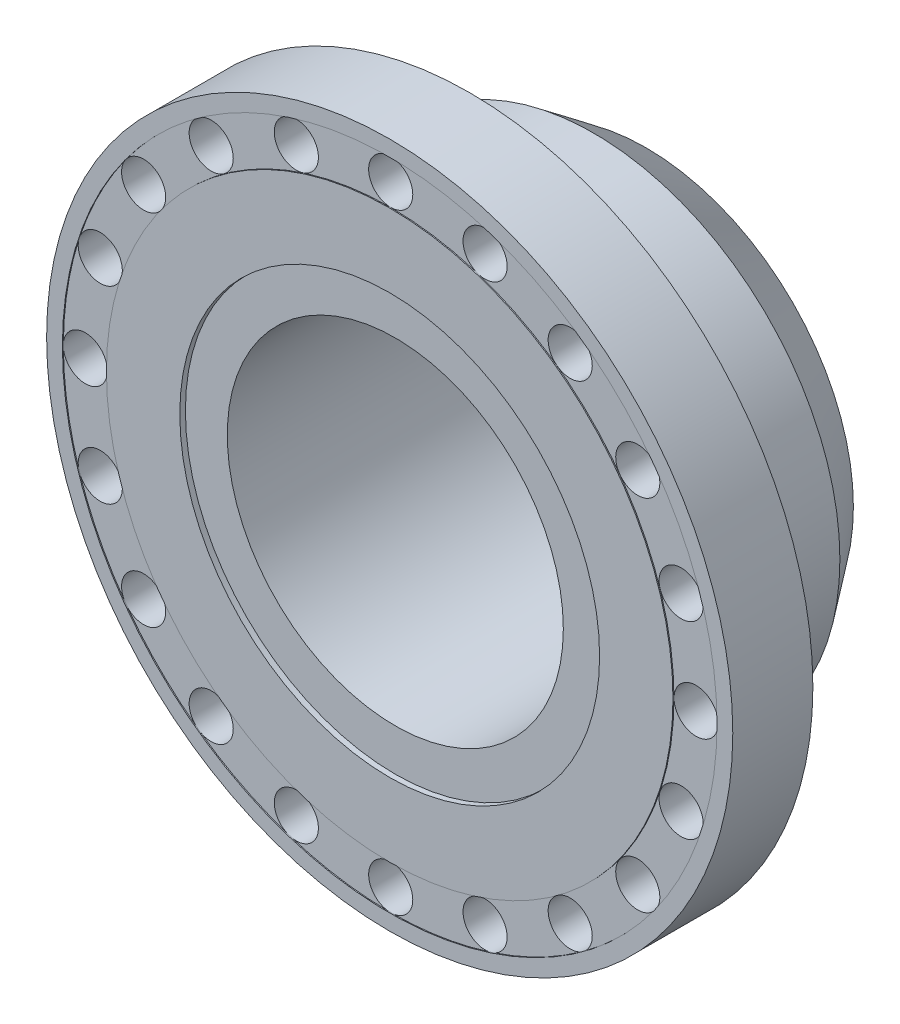
SolidWorks part; units mm, degrees
material "Alloy Steel"
ref_plane "Front Plane" through (0, 0, 0) normal (0, 0, 1) x (1, 0, 0)
ref_plane "Top Plane" through (0, 0, 0) normal (0, 1, 0) x (1, 0, 0)
ref_plane "Right Plane" through (0, 0, 0) normal (1, 0, 0) x (0, 0, -1)
sketch "Sketch1" plane through (0, 0, 0) normal (0, 0, 1) x (1, 0, 0)
  circle A0 centre (0, 0) radius 456.6196
extrude "Extrude1" add sketch "Sketch1" against normal blind 106.5987
sketch "Sketch2" plane through (0, 0, 0) normal (0, 0, 1) x (1, 0, 0)
  circle A0 centre (0, 0) radius 279.381
extrude "Extrude2" cut sketch "Sketch2" against normal blind 7.4651
sketch "Sketch3" plane through (0, 0, -106.5987) normal (0, 0, -1) x (-1, 0, 0)
  circle A1 centre (0, 0) radius 327.7006
extrude "Extrude3" add sketch "Sketch3" along normal blind 234.7316
chamfer "Chamfer1" distance 69.85 distance2 51.896 1 edges at (-327.7006, 0, -341.3303)
sketch "Sketch4" plane through (0, 0, -7.4651) normal (0, 0, 1) x (1, 0, 0)
  circle A0 centre (0, 0) radius 223.6305
extrude "Extrude4" cut sketch "Sketch4" against normal blind 333.8652
sketch "Sketch5" plane through (0, 0, 0) normal (0, 0, 1) x (1, 0, 0)
  circle A0 centre (0, 0) radius 435.6278
  circle A1 centre (0, 0) radius 377.0211
extrude "Extrude5" cut sketch "Sketch5" against normal blind 1.3449
sketch "Sketch6" plane through (0, 0, -1.3449) normal (0, 0, 1) x (1, 0, 0)
  circle A1 centre (0, 406.4419) radius 29.3688
extrude "Extrude6" cut sketch "Sketch6" against normal blind 105.7173
pattern_circular "CirPattern1" count 20 over 360 about axis through (0, 0, 0) along (0, 0, 1) of "Extrude6"
chamfer "Chamfer2" distance 6.35 angle 45 1 edges at (223.6305, 0, -341.3303)
